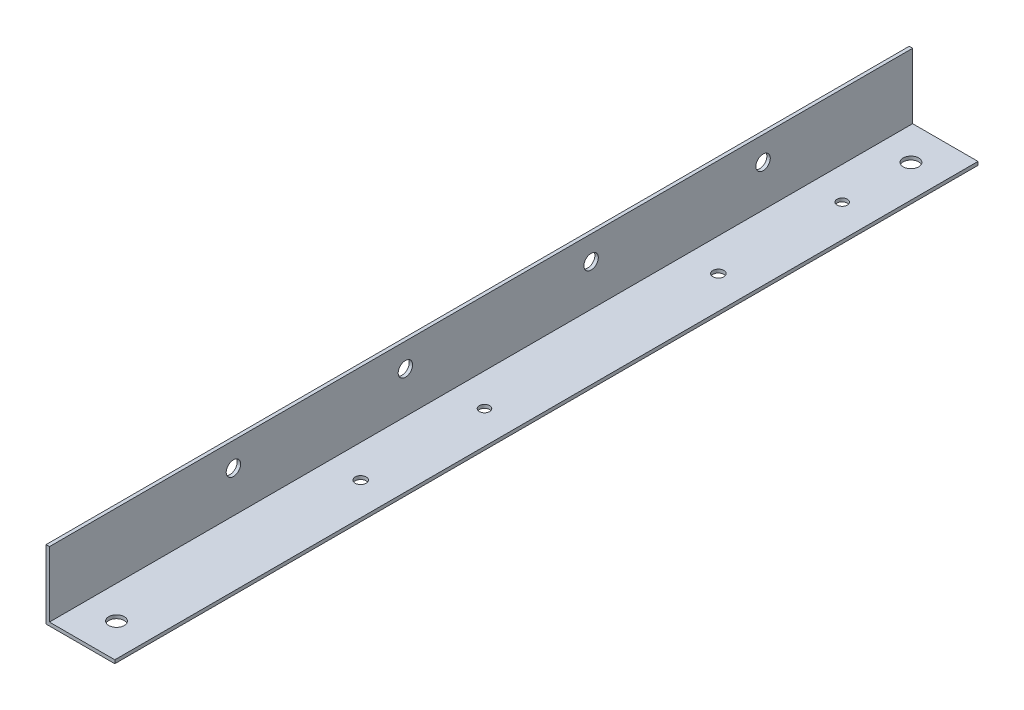
SolidWorks part; units mm, degrees
material "1060 Сплав"
ref_plane "Спереди" through (0, 0, 0) normal (0, 0, 1) x (1, 0, 0)
ref_plane "Сверху" through (0, 0, 0) normal (0, 1, 0) x (1, 0, 0)
ref_plane "Справа" through (0, 0, 0) normal (1, 0, 0) x (0, 0, -1)
sketch "Эскиз1" plane through (0, 0, 0) normal (0, 0, 1) x (1, 0, 0)
  line L0 (0, 0) -> (0, 20)
  line L1 (0, 20) -> (1, 20)
  line L2 (1, 20) -> (1, 1)
  line L3 (1, 1) -> (20, 1)
  line L4 (20, 1) -> (20, 0)
  line L5 (20, 0) -> (0, 0)
  dimension "D1" = 20
  dimension "D2" = 1
extrude "Бобышка-Вытянуть1" add sketch "Эскиз1" along normal blind 251
sketch "Эскиз2" plane through (0, 1, 0) normal (0, 1, 0) x (1, 0, 0)
  line L0 (10.5, 0) -> (10.5, -251) construction
  line L1 (20, 0) -> (1, 0) construction
  line L2 (20, -251) -> (1, -251) construction
ref_plane "Плоскость1" through (10.5, 0, 0) normal (-1, 0, 0) x (0, 0, 1)
sketch "Эскиз3" plane through (0, 1, 0) normal (0, 1, 0) x (1, 0, 0)
  circle A0 centre (10.5, -134) radius 1.5 construction
  circle A1 centre (10.5, -134) radius 1.5
  circle A2 centre (10.5, -170) radius 1.6 construction
  circle A3 centre (10.5, -170) radius 1.6
  circle A4 centre (10.5, -66) radius 1.6 construction
  circle A5 centre (10.5, -66) radius 1.6
  circle A6 centre (10.5, -30) radius 1.5 construction
  circle A7 centre (10.5, -30) radius 1.5
extrude "Вырез-Вытянуть1" cut sketch "Эскиз3" against normal through all
sketch "Эскиз4" plane through (0, 0, 0) normal (-1, 0, 0) x (0, 0, 1)
  line L0 (63.5, 27) -> (63.5, 0) construction
  line L1 (251, 0) -> (0, 0) construction
  line L2 (167.5, 27) -> (167.5, 0) construction
  line L3 (0, 13) -> (251, 13) construction
  line L4 (130, 25) -> (205, 25)
  line L5 (205, 25) -> (205, 27)
  line L6 (205, 27) -> (130, 27)
  line L7 (130, 27) -> (130, 25)
  line L8 (130, 25) -> (205, 25) construction
  line L9 (205, 25) -> (205, 27) construction
  line L10 (205, 27) -> (130, 27) construction
  line L11 (130, 27) -> (130, 25) construction
  line L12 (26, 25) -> (101, 25)
  line L13 (101, 25) -> (101, 27)
  line L14 (101, 27) -> (26, 27)
  line L15 (26, 27) -> (26, 25)
  line L16 (26, 25) -> (101, 25) construction
  line L17 (101, 25) -> (101, 27) construction
  line L18 (101, 27) -> (26, 27) construction
  line L19 (26, 27) -> (26, 25) construction
  line L20 (0, 20) -> (0, 0) construction
  line L21 (251, 20) -> (251, 0) construction
  line L22 (251, 20) -> (0, 20) construction
  circle A0 centre (43.5, 13) radius 2.1
  circle A1 centre (93.5, 13) radius 2.1
  circle A2 centre (147.5, 13) radius 2.1
  circle A3 centre (197.5, 13) radius 2.1
  dimension "D4" = 4.2
  dimension "D5" = 50
  dimension "D6" = 50
  dimension "D8" = 20
  dimension "D3" = 7
  dimension "D7" = 20
  dimension "D1" = 0
  dimension "D2" = 0
extrude "Вырез-Вытянуть2" cut sketch "Эскиз4" against normal through all
sketch "Эскиз5" plane through (0, 1, 0) normal (0, 1, 0) x (1, 0, 0)
  line L0 (10.5, -251) -> (10.5, 0) construction
  line L1 (20, -251) -> (1, -251) construction
  line L2 (20, 0) -> (1, 0) construction
  circle A0 centre (10.5, -10) radius 2.25
  circle A1 centre (10.5, -241) radius 2.25
  dimension "D1" = 4.5
  dimension "D3" = 4.5
  dimension "D4" = 10
  dimension "D2" = 10
extrude "Вырез-Вытянуть3" cut sketch "Эскиз5" against normal through all
